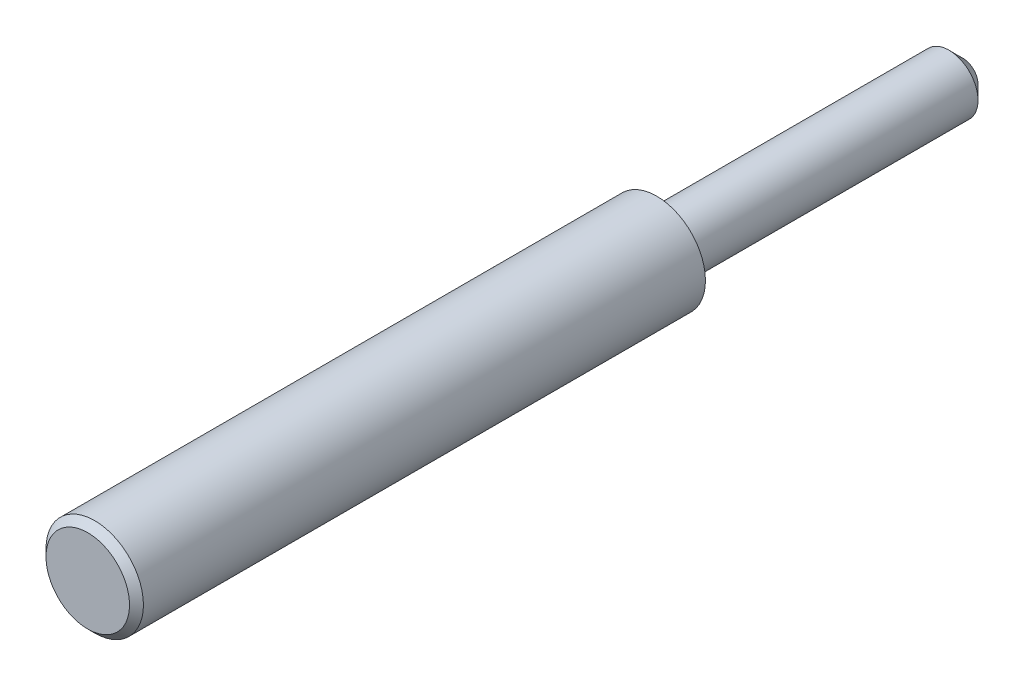
SolidWorks part; units mm, degrees
material "6061-T6 (SS)"
ref_plane "Front" through (0, 0, 0) normal (0, 0, 1) x (1, 0, 0)
ref_plane "Top" through (0, 0, 0) normal (0, 1, 0) x (1, 0, 0)
ref_plane "Right" through (0, 0, 0) normal (1, 0, 0) x (0, 0, -1)
sketch "Sketch1" plane through (0, 0, 0) normal (1, 0, 0) x (0, 0, -1)
  line L0 (0, 0) -> (45.8519, 0) construction
  line L1 (0, 0) -> (0, 50.0751) construction
  line L2 (22, 0) -> (22, 2.0828)
  line L3 (22, 2.0828) -> (0, 2.0828)
  line L4 (0, 2.0828) -> (0, 3.5)
  line L5 (0, 3.5) -> (-40.879, 3.5)
  line L6 (-40.879, 3.5) -> (-40.879, 0)
  line L7 (-40.879, 0) -> (22, 0)
  dimension "D1" = 22
  dimension "D2" = 4.1656
  dimension "D3" = 7
  dimension "D4" = 40.879
revolve "Revolve1" add sketch "Sketch1" angle 360 about L0
cosmetic thread "Cosmetic Thread1 8-32"
chamfer "Chamfer1" distance 1 angle 45 1 edges at (2.0828, 0, -22)
chamfer "Chamfer2" distance 0.5 angle 45 1 edges at (3.5, 0, 40.879)
